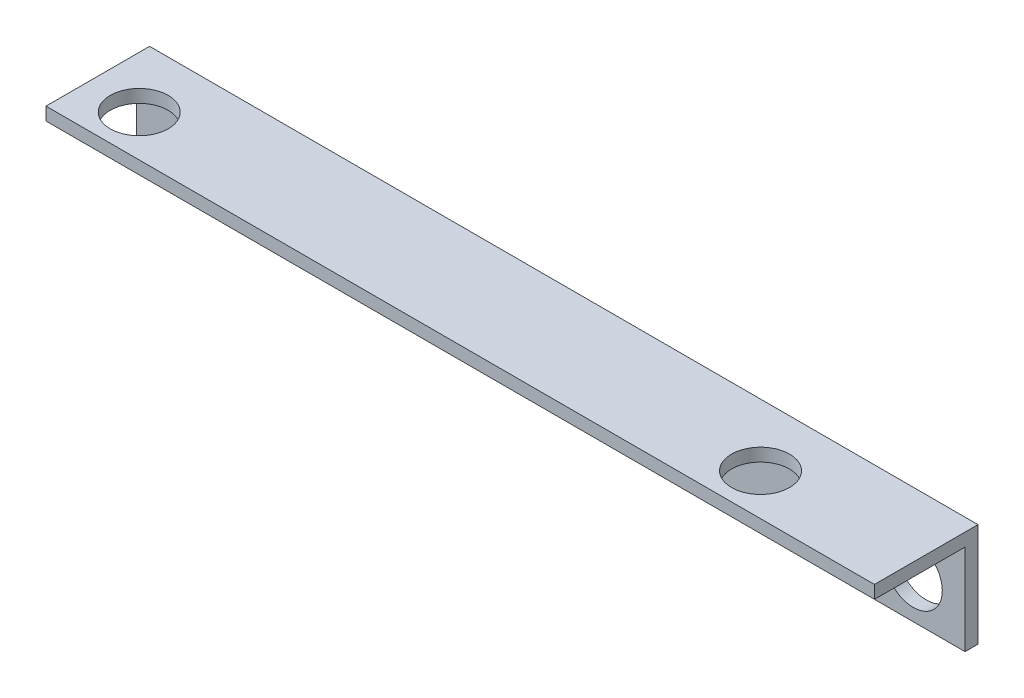
SolidWorks part; units mm, degrees
material "5052-H32"
ref_plane "Front Plane" through (0, 0, 0) normal (0, 0, 1) x (1, 0, 0)
ref_plane "Top Plane" through (0, 0, 0) normal (0, 1, 0) x (1, 0, 0)
ref_plane "Right Plane" through (0, 0, 0) normal (1, 0, 0) x (0, 0, -1)
sketch "Sketch1" plane through (0, 0, 0) normal (1, 0, 0) x (0, 0, -1)
  line L0 (0, 0) -> (0, 12.7)
  line L1 (0, 55) -> (0, -55) construction
  line L11 (0, 12.7) -> (-12.7, 12.7)
  line L13 (-1.5875, 0) -> (-1.5875, 11.1125)
  line L14 (-1.5875, 11.1125) -> (-12.7, 11.1125)
  line L15 (-12.7, 11.1125) -> (-12.7, 12.7)
  line L16 (-1.5875, 0) -> (0, 0)
  dimension "D1" = 1.5875
  dimension "D2" = 12.7
  dimension "D3" = 11.1125
extrude "Boss-Extrude1" add sketch "Sketch1" along normal blind 57.15 and the other way blind 44.45
sketch "Sketch3" plane through (0, 0, 0) normal (0, 0, -1) x (-1, 0, 0)
  line L1 (-57.15, 0) -> (-57.15, 12.7) construction
  line L2 (25.4, 5.08) -> (-50.8, 5.08) construction
  line L3 (44.45, 12.7) -> (-57.15, 12.7) construction
  circle A0 centre (25.4, 5.08) radius 3.556
  circle A1 centre (-50.8, 5.08) radius 3.556
  dimension "D1" = 7.112
  dimension "D2" = 7.62
  dimension "D3" = 76.2
  dimension "D4" = 6.35
extrude "Cut-Extrude1" cut sketch "Sketch3" against normal through all
sketch "Sketch4" plane through (0, 12.7, 0) normal (0, 1, 0) x (1, 0, 0)
  line L0 (-38.1, -7.62) -> (38.1, -7.62) construction
  line L1 (-44.45, 0) -> (-44.45, -12.7) construction
  line L2 (-6.985, 0) -> (6.985, 0) construction
  circle A0 centre (-38.1, -7.62) radius 3.556
  circle A1 centre (38.1, -7.62) radius 3.556
  dimension "D1" = 7.112
  dimension "D2" = 76.2
  dimension "D3" = 6.35
  dimension "D4" = 7.62
extrude "Cut-Extrude2" cut sketch "Sketch4" against normal through all
